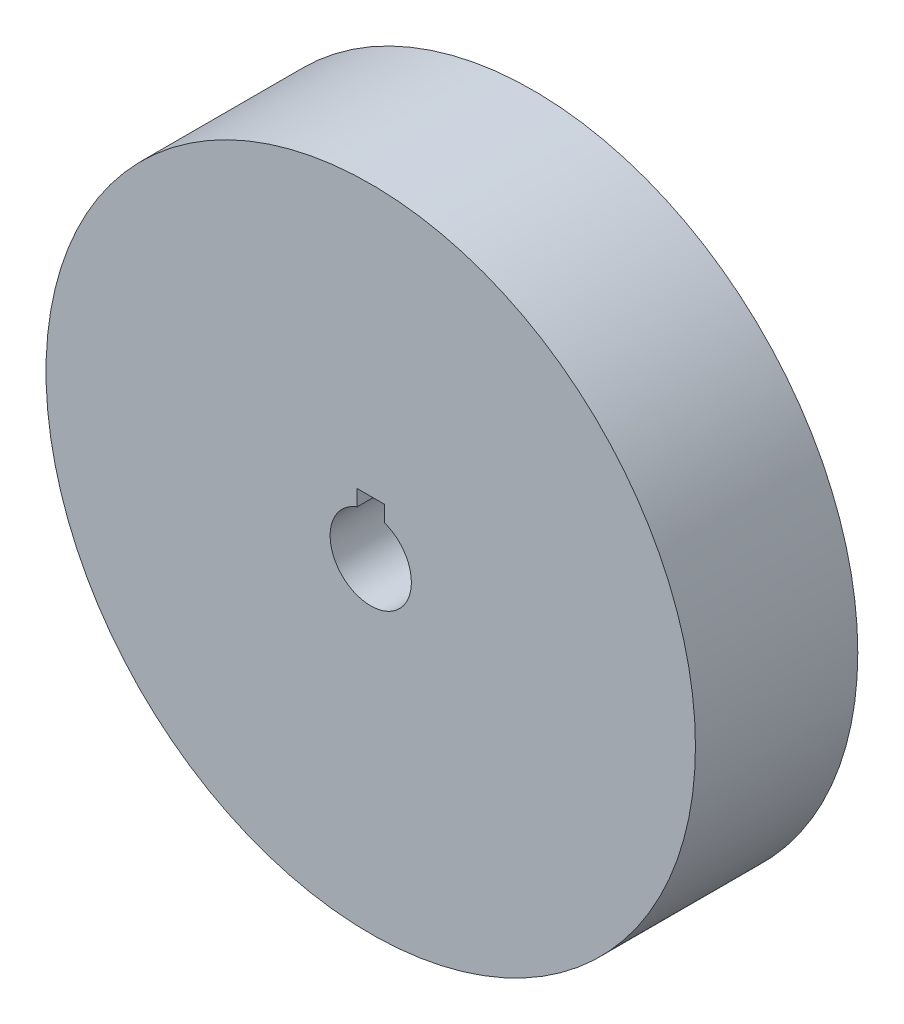
SolidWorks part; units mm, degrees
ref_plane "Front Plane" through (0, 0, 0) normal (0, 0, 1) x (1, 0, 0)
ref_plane "Top Plane" through (0, 0, 0) normal (0, 1, 0) x (1, 0, 0)
ref_plane "Right Plane" through (0, 0, 0) normal (1, 0, 0) x (0, 0, -1)
sketch "Sketch1" plane through (0, 0, 0) normal (0, 0, 1) x (1, 0, 0)
  line L1 (-3.1877, 6.35) -> (3.1877, 6.35)
  line L2 (-3.1877, 6.35) -> (-3.1877, 12.7254)
  line L3 (-3.1877, 12.7254) -> (3.1877, 12.7254)
  line L4 (3.1877, 6.35) -> (3.1877, 12.7254)
  line L5 (-3.1877, 6.35) -> (3.1877, 12.7254) construction
  line L6 (-3.1877, 12.7254) -> (3.1877, 6.35) construction
  circle A0 centre (0, 0) radius 76.2
  circle A1 centre (0, 0) radius 9.5377
  point P4 (0, 9.5377)
  dimension "D1" = 152.4
  dimension "D2" = 19.0754
  dimension "D3" = 6.3754
extrude "Boss-Extrude1" add sketch "Sketch1" along normal blind 38.1 contours A0 A1 L2 L3 L4
